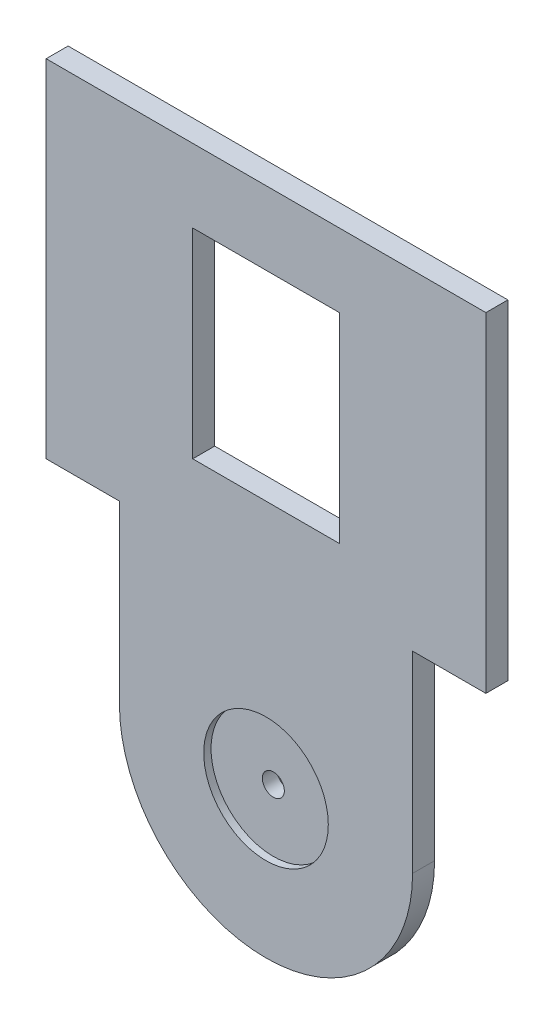
SolidWorks part; units mm, degrees
ref_plane "Alzado" through (0, 0, 0) normal (0, 0, 1) x (1, 0, 0)
ref_plane "Planta" through (0, 0, 0) normal (0, 1, 0) x (1, 0, 0)
ref_plane "Vista lateral" through (0, 0, 0) normal (1, 0, 0) x (0, 0, -1)
sketch "Croquis1" plane through (0, 0, 0) normal (0, 0, 1) x (1, 0, 0)
  line L0 (-113.9918, 10.9708) -> (-73.9918, 10.9708) construction
  line L1 (-113.9918, 10.9708) -> (-113.9918, 34.9581)
  line L2 (-113.9918, 34.9581) -> (-123.9918, 34.9581)
  line L3 (-123.9918, 34.9581) -> (-123.9918, 82.2366)
  line L4 (-123.9918, 82.2366) -> (-63.9918, 82.2366)
  line L5 (-73.9918, 10.9708) -> (-73.9918, 37.2366)
  line L6 (-73.9918, 37.2366) -> (-63.9918, 37.2366)
  line L7 (-63.9918, 37.2366) -> (-63.9918, 82.2366)
  line L9 (-103.9918, 72.2366) -> (-83.9918, 72.2366)
  line L10 (-103.9918, 72.2366) -> (-103.9918, 44.9581)
  line L11 (-103.9918, 44.9581) -> (-83.9918, 44.9581)
  line L12 (-83.9918, 72.2366) -> (-83.9918, 44.9581)
  arc A0 (-113.9918, 10.9708) -> (-73.9918, 10.9708) centre (-93.9918, 10.9708) ccw
  circle A1 centre (-93.9918, 10.9708) radius 1.5
  dimension "D1" = 20
  dimension "D6" = 3
  dimension "D2" = 20
  dimension "D3" = 60
  dimension "D4" = 10
  dimension "D5" = 10
  dimension "D7" = 10
  dimension "D8" = 45
  dimension "D9" = 10
extrude "Saliente-Extruir1" add sketch "Croquis1" along normal blind 3
sketch "Croquis2" plane through (0, 0, 3) normal (0, 0, 1) x (1, 0, 0)
  circle A0 centre (-93.9918, 10.9708) radius 8.5
extrude "Cortar-Extruir1" cut sketch "Croquis2" against normal blind 1
